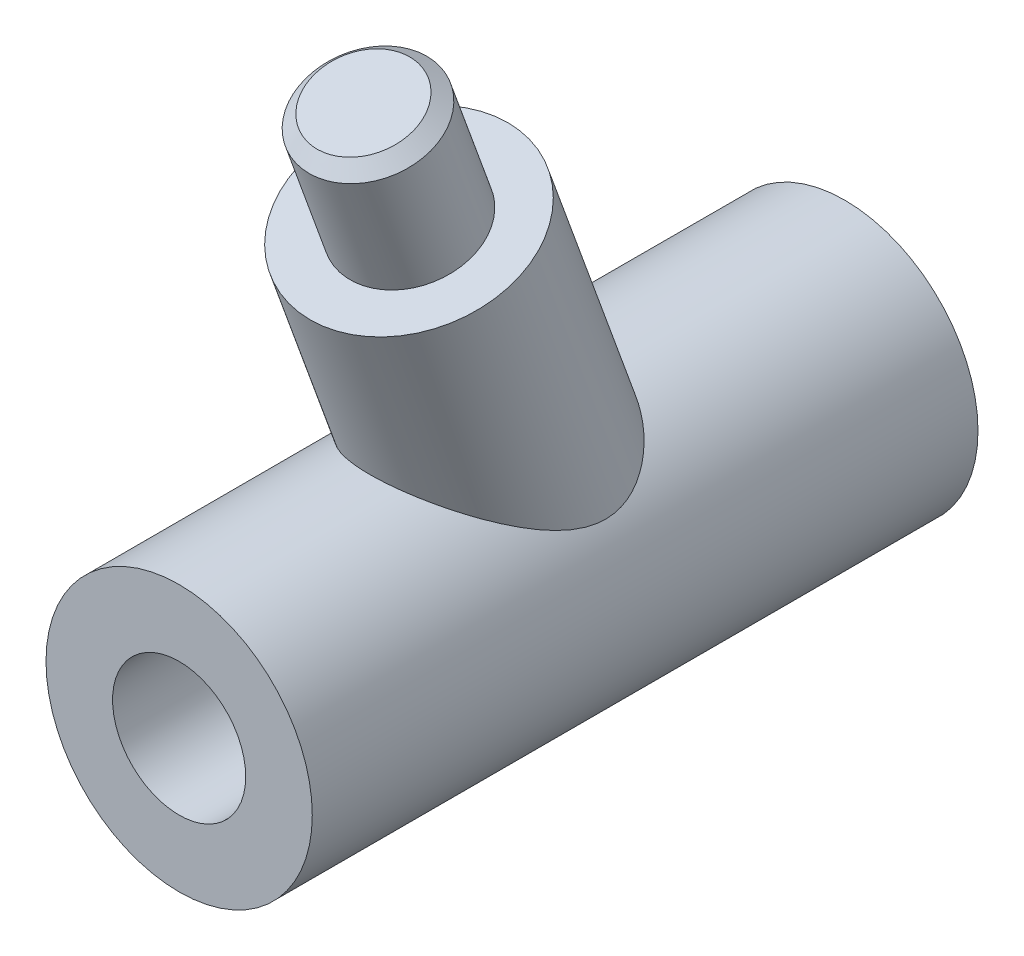
SolidWorks part; units mm, degrees
ref_plane "Front Plane" through (0, 0, 0) normal (0, 0, 1) x (1, 0, 0)
ref_plane "Top Plane" through (0, 0, 0) normal (0, 1, 0) x (1, 0, 0)
ref_plane "Right Plane" through (0, 0, 0) normal (1, 0, 0) x (0, 0, -1)
sketch "Sketch1" plane through (0, 0, 0) normal (0, 0, 1) x (1, 0, 0)
  circle A0 centre (0, 0) radius 10
  circle A1 centre (0, 0) radius 5
  dimension "D1" = 20
  dimension "D2" = 10
extrude "Boss-Extrude1" add sketch "Sketch1" along normal blind 50
sketch "Sketch3" plane through (0, 0, 0) normal (1, 0, 0) x (0, 0, -1)
  line L2 (-32.739, 25) -> (-20, -10)
  line L3 (-50, -10) -> (0, -10) construction
  line L4 (-20, -10) -> (-50, -10)
  line L5 (-50, 10) -> (-50, -10) construction
  point P12 (-34.5145, 22.9889)
  dimension "D1" = 30
  dimension "D2" = 70
  dimension "D3" = 35
ref_plane "Plane2" through (0, 25, 32.739) normal (0, -0.9397, -0.342) x (-1, 0, 0)
sketch "Sketch4" plane through (0, 25, 32.739) normal (0, -0.9397, -0.342) x (-1, 0, 0)
  circle A0 centre (0, 0) radius 7.9
  dimension "D1" = 15.8
extrude "Boss-Extrude2" add sketch "Sketch4" along normal up to surface (18.838 mm away)
sketch "Sketch6" plane through (0, 32.5977, 11.8646) normal (0, 0.9397, 0.342) x (1, 0, 0)
  circle A0 centre (0, -22.2141) radius 4.7
  dimension "D1" = 9.4
extrude "Boss-Extrude3" add sketch "Sketch6" along normal blind 10
chamfer "Chamfer1" distance 1 angle 45 1 edges at (0, 32.7894, 40.5757)
